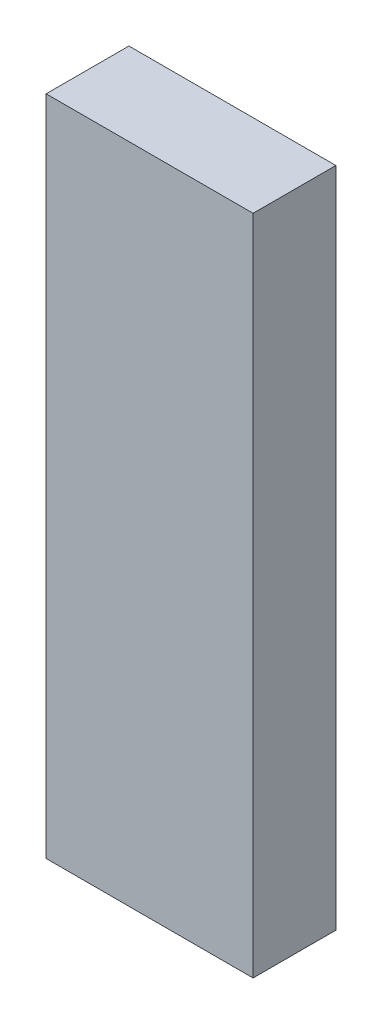
SolidWorks part; units mm, degrees
ref_plane "Front Plane" through (0, 0, 0) normal (0, 0, 1) x (1, 0, 0)
ref_plane "Top Plane" through (0, 0, 0) normal (0, 1, 0) x (1, 0, 0)
ref_plane "Right Plane" through (0, 0, 0) normal (1, 0, 0) x (0, 0, -1)
sketch "Sketch1" plane through (0, 0, 0) normal (0, 1, 0) x (1, 0, 0)
  line L1 (-31.75, -12.7) -> (31.75, -12.7)
  line L2 (-31.75, -12.7) -> (-31.75, 12.7)
  line L3 (-31.75, 12.7) -> (31.75, 12.7)
  line L4 (31.75, -12.7) -> (31.75, 12.7)
  line L5 (-31.75, -12.7) -> (31.75, 12.7) construction
  line L6 (-31.75, 12.7) -> (31.75, -12.7) construction
  point P0 (0, 0)
  dimension "D1" = 63.5
  dimension "D2" = 25.4
extrude "Boss-Extrude1" add sketch "Sketch1" along normal mid plane 203.2
